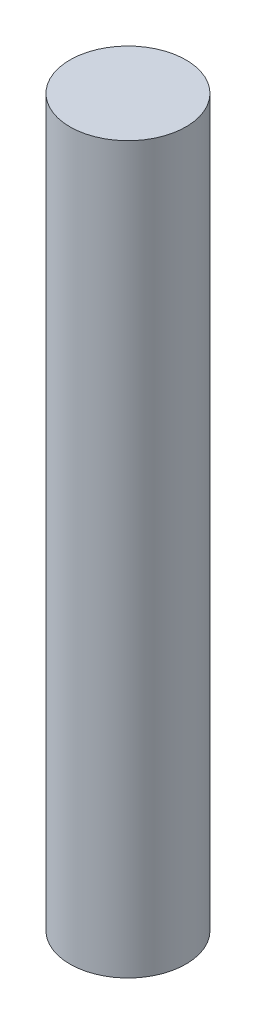
SolidWorks part; units mm, degrees
ref_plane "前视基准面" through (0, 0, 0) normal (0, 0, 1) x (1, 0, 0)
ref_plane "上视基准面" through (0, 0, 0) normal (0, 1, 0) x (1, 0, 0)
ref_plane "右视基准面" through (0, 0, 0) normal (1, 0, 0) x (0, 0, -1)
sketch "草图2" plane through (0, 0, 0) normal (0, 1, 0) x (1, 0, 0)
  circle A0 centre (0, 0) radius 4
  dimension "D1" = 8
extrude "凸台-拉伸1" [suppressed] add sketch "草图2" along normal blind 20 contours A0
sketch "草图3" plane through (0, 0, 0) normal (0, 1, 0) x (1, 0, 0)
  circle A0 centre (0, 0) radius 4
  dimension "D1" = 8
extrude "凸台-拉伸2" add sketch "草图3" along normal blind 50
sketch "草图4" [suppressed] plane through (0, 0, 0) normal (0, 1, 0) x (1, 0, 0)
  circle A0 centre (0, 0) radius 4
  dimension "D1" = 8
extrude "凸台-拉伸3" [suppressed] add sketch "草图4" along normal blind 15
